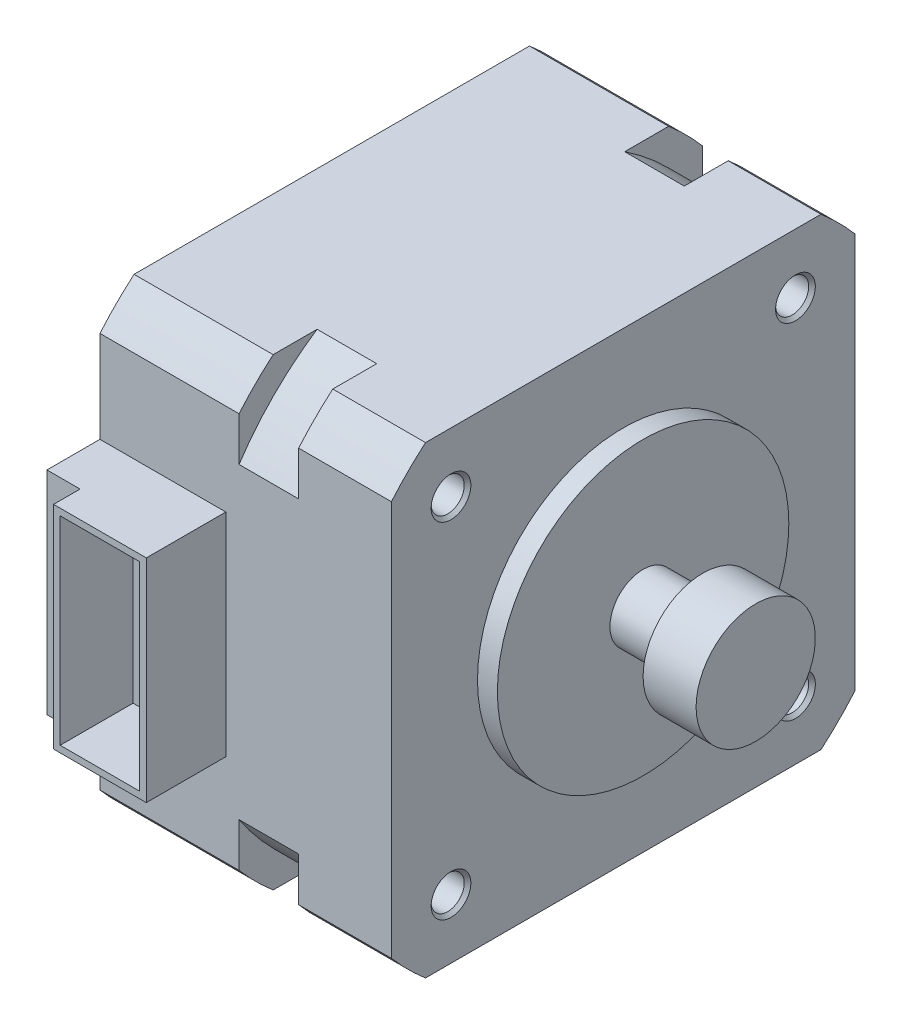
SolidWorks part; units mm, degrees
ref_plane "Front Plane" through (0, 0, 0) normal (0, 0, 1) x (1, 0, 0)
ref_plane "Top Plane" through (0, 0, 0) normal (0, 1, 0) x (1, 0, 0)
ref_plane "Right Plane" through (0, 0, 0) normal (1, 0, 0) x (0, 0, -1)
ref_plane "Plane1" through (0, 0, 0) normal (-1, 0, 0) x (0, -1, 0)
sketch "Sketch1" plane through (0, 0, 0) normal (-1, 0, 0) x (0, -1, 0)
  line L0 (14.9248, 17.5) -> (-14.9248, 17.5)
  line L1 (-17.5, 14.9248) -> (-17.5, -14.9248)
  line L2 (-14.9248, -17.5) -> (14.9248, -17.5)
  line L3 (17.5, -14.9248) -> (17.5, 14.9248)
  arc A0 (17.5, 14.9248) -> (14.9248, 17.5) centre (0, 0) ccw
  arc A1 (-14.9248, 17.5) -> (-17.5, 14.9248) centre (0, 0) ccw
  arc A2 (-17.5, -14.9248) -> (-14.9248, -17.5) centre (0, 0) ccw
  arc A3 (14.9248, -17.5) -> (17.5, -14.9248) centre (0, 0) ccw
extrude "Boss-Extrude1" add sketch "Sketch1" against normal blind 10.5
sketch "Sketch2" plane through (10.5, 0, 0) normal (1, 0, 0) x (0, 0, -1)
  line L0 (-17.5, -11.6082) -> (-17.5, 11.6082)
  line L1 (-11.6082, 17.5) -> (11.6082, 17.5)
  line L2 (17.5, 11.6082) -> (17.5, -11.6082)
  line L3 (11.6082, -17.5) -> (-11.6082, -17.5)
  arc A0 (-17.5, 11.6082) -> (-11.6082, 17.5) centre (0, 0) cw
  arc A1 (11.6082, 17.5) -> (17.5, 11.6082) centre (0, 0) cw
  arc A2 (17.5, -11.6082) -> (11.6082, -17.5) centre (0, 0) cw
  arc A3 (-11.6082, -17.5) -> (-17.5, -11.6082) centre (0, 0) cw
extrude "Boss-Extrude2" add sketch "Sketch2" along normal blind 4.5
sketch "Sketch3" plane through (15, 0, 0) normal (1, 0, 0) x (0, 0, -1)
  line L0 (17.5, 14.9248) -> (17.5, -14.9248)
  line L1 (14.9248, -17.5) -> (-14.9248, -17.5)
  line L2 (-17.5, -14.9248) -> (-17.5, 14.9248)
  line L3 (-14.9248, 17.5) -> (14.9248, 17.5)
  arc A0 (17.5, -14.9248) -> (14.9248, -17.5) centre (0, 0) cw
  arc A1 (-14.9248, -17.5) -> (-17.5, -14.9248) centre (0, 0) cw
  arc A2 (-17.5, 14.9248) -> (-14.9248, 17.5) centre (0, 0) cw
  arc A3 (14.9248, 17.5) -> (17.5, 14.9248) centre (0, 0) cw
extrude "Boss-Extrude3" add sketch "Sketch3" along normal blind 7
sketch "Sketch4" plane through (0, 0, 17.5) normal (0, 0, 1) x (1, 0, 0)
  line L0 (9.5, 8) -> (9.5, -8)
  line L1 (9.5, -8) -> (0, -8)
  line L2 (0, -8) -> (0, 8)
  line L3 (0, 8) -> (9.5, 8)
extrude "Boss-Extrude4" add sketch "Sketch4" along normal blind 6
sketch "Sketch5" plane through (0, -8, 0) normal (0, -1, 0) x (1, 0, 0)
  line L0 (2.5, 21.5) -> (2.5, 23.5)
  line L1 (2.5, 23.5) -> (0, 23.5)
  line L2 (0, 23.5) -> (0, 21.5)
  line L3 (0, 21.5) -> (2.5, 21.5)
extrude "Cut-Extrude1" cut sketch "Sketch5" against normal through all
sketch "Sketch6" plane through (0, 0, 23.5) normal (0, 0, 1) x (1, 0, 0)
  line L0 (3, -7.5) -> (9, -7.5)
  line L1 (9, -7.5) -> (9, 7.5)
  line L2 (9, 7.5) -> (3, 7.5)
  line L3 (3, 7.5) -> (3, -7.5)
extrude "Cut-Extrude2" cut sketch "Sketch6" against normal blind 5.5
ref_plane "Plane2" through (0, 0, 0) normal (0, 0, -1) x (-1, 0, 0)
sketch "Sketch7" plane through (0, 0, 0) normal (0, 0, -1) x (-1, 0, 0)
  line L0 (-32, 4.5) -> (-32, 0)
  line L1 (-32, 0) -> (-22, 0)
  line L2 (-22, 0) -> (-22, 11)
  line L3 (-22, 11) -> (-23.5, 11)
  line L4 (-23.5, 11) -> (-23.5, 2.5)
  line L5 (-23.5, 2.5) -> (-28, 2.5)
  line L6 (-28, 2.5) -> (-28, 4.5)
  line L7 (-28, 4.5) -> (-32, 4.5)
  line L8 (-32, 0) -> (-22, 0) construction
revolve "Revolve1" add sketch "Sketch7" angle 360 about L8
hole_wizard "#2 Clearance Hole1" positions "Sketch9" profile "Sketch8" hole size "#2" standard "ANSI Inch"
sketch "Sketch9" plane through (22, 0, 0) normal (1, 0, 0) x (0, 0, -1)
  point P0 (-13, 13)
  point P1 (13, 13)
  point P2 (13, -13)
  point P3 (-13, -13)
sketch "Sketch8" plane through (22, 13, 13) normal (0, 1, 0) x (0, 0, -1)
  line L0 (0, 0) -> (0, 22)
  line L1 (0, 22) -> (1.25, 22)
  line L2 (1.25, 22) -> (1.25, 0)
  line L5 (1.25, 0) -> (0, 0)
  line L11 (0, -6.35) -> (0, 107.95) construction
  dimension "Thru Hole Dia." = 2.5
  dimension "Thru Hole Depth" = 22
chamfer "Chamfer1" distance 0.25 angle 45 8 edges at (0, -13, 11.75) (0, 13, -14.25) (0, 13, 11.75) (22, 13, -14.25) (0, -13, -14.25) (22, -13, -14.25) (22, 13, 11.75) (22, -13, 11.75)
